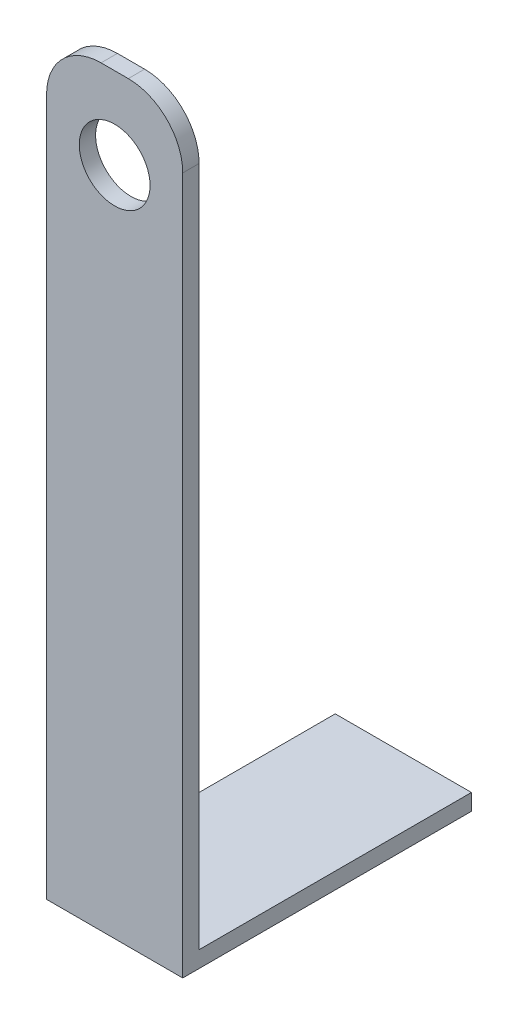
SolidWorks part; units mm, degrees
material "AISI 1030 HR"
ref_plane "Alzado" through (0, 0, 0) normal (0, 0, 1) x (1, 0, 0)
ref_plane "Planta" through (0, 0, 0) normal (0, 1, 0) x (1, 0, 0)
ref_plane "Vista lateral" through (0, 0, 0) normal (1, 0, 0) x (0, 0, -1)
sketch "Croquis1" plane through (0, 0, 0) normal (0, 1, 0) x (1, 0, 0)
  line L1 (-25, -50) -> (25, -50)
  line L2 (-25, -50) -> (-25, 50)
  line L3 (-25, 50) -> (25, 50)
  line L4 (25, -50) -> (25, 50)
  line L5 (-25, -50) -> (25, 50) construction
  line L6 (-25, 50) -> (25, -50) construction
  point P0 (0, 0)
  dimension "D1" = 50
  dimension "D2" = 100
extrude "Saliente-Extruir1" add sketch "Croquis1" along normal blind 6
sketch "Croquis2" plane through (0, 0, 0) normal (0, -1, 0) x (1, 0, 0)
  line L1 (25, 50) -> (-25, 50)
  line L2 (25, 50) -> (25, 56)
  line L3 (25, 56) -> (-25, 56)
  line L4 (25, -50) -> (25, 50)
  line L5 (25, 50) -> (-25, 50)
  line L6 (-25, 50) -> (-25, -50)
  line L7 (-25, -50) -> (25, -50)
  line L8 (25, -50) -> (25, 50)
  line L9 (25, 50) -> (-25, 50)
  line L10 (-25, 50) -> (-25, -50)
  line L11 (-25, -50) -> (25, -50)
  line L12 (-25, 50) -> (-25, 56)
  line M10 (25, 50) -> (-25, 50)
  dimension "D2" = 6
  dimension "D1" = 0
extrude "Saliente-Extruir2" add sketch "Croquis2" against normal blind 276 contours L12 L2 L3 M10
sketch "Croquis3" plane through (0, 0, 56) normal (0, 0, 1) x (1, 0, 0)
  line L0 (25, 276) -> (25, 0) construction
  line L1 (25, 276) -> (-25, 276) construction
  circle A0 centre (0, 246) radius 13
  dimension "D1" = 26
  dimension "D2" = 25
  dimension "D3" = 30
extrude "Cortar-Extruir1" cut sketch "Croquis3" against normal blind 6
fillet "Redondeo1" radius 20 2 edges at (25, 276, 53) (-25, 276, 53)
